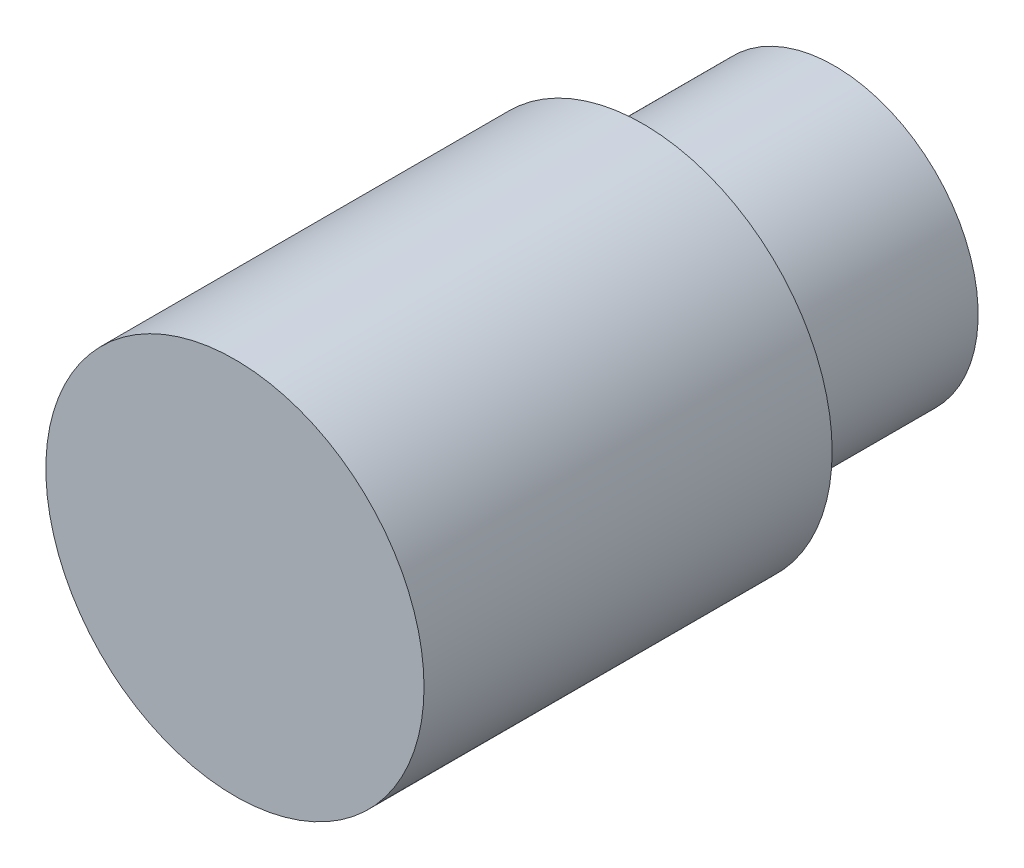
SolidWorks part; units mm, degrees
ref_plane "Спереди" through (0, 0, 0) normal (0, 0, 1) x (1, 0, 0)
ref_plane "Сверху" through (0, 0, 0) normal (0, 1, 0) x (1, 0, 0)
ref_plane "Справа" through (0, 0, 0) normal (1, 0, 0) x (0, 0, -1)
sketch "Эскиз1" plane through (0, 0, 0) normal (0, 0, 1) x (1, 0, 0)
  circle A0 centre (0, 0) radius 7.9 construction
  circle A1 centre (0, 0) radius 7.9
extrude "Бобышка-Вытянуть1" add sketch "Эскиз1" against normal up to surface (17.05 mm away)
sketch "Эскиз2" plane through (0, 0, -17.05) normal (0, 0, -1) x (-1, 0, 0)
  circle A0 centre (-0.0002, 0.0002) radius 6 construction
  circle A1 centre (-0.0002, 0.0002) radius 6
extrude "Бобышка-Вытянуть2" add sketch "Эскиз2" along normal up to surface (8 mm away)
